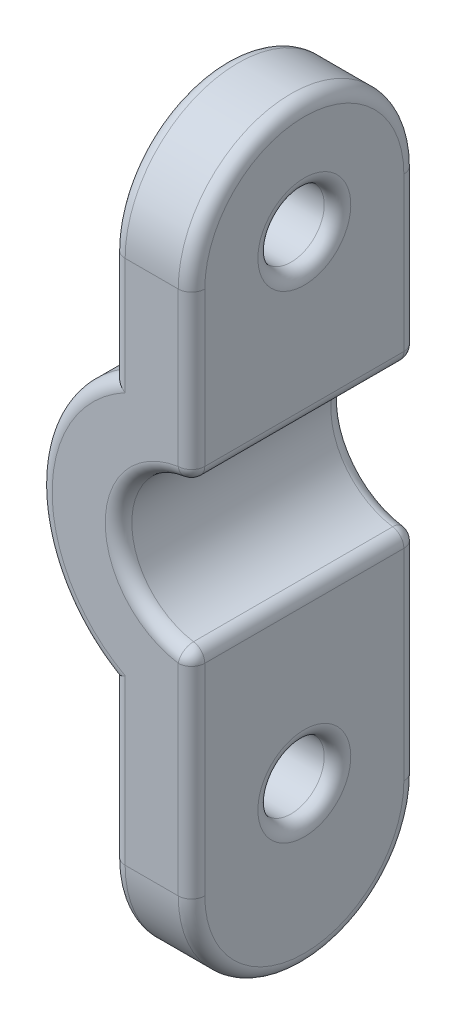
SolidWorks part; units mm, degrees
ref_plane "Front Plane" through (0, 0, 0) normal (0, 0, 1) x (1, 0, 0)
ref_plane "Top Plane" through (0, 0, 0) normal (0, 1, 0) x (1, 0, 0)
ref_plane "Right Plane" through (0, 0, 0) normal (1, 0, 0) x (0, 0, -1)
sketch "Sketch1" plane through (0, 0, 0) normal (0, 0, 1) x (1, 0, 0)
  line L0 (-2.75, 16.15) -> (-2.75, -14.35) construction
  line L1 (-2.75, -14.35) -> (-2.75, -1.85)
  line L6 (0.75, 11.15) -> (-2.75, 11.15) construction
  line L8 (1, 11.15) -> (0.5, 11.15) construction
  line L9 (-2.75, 16.15) -> (-5.75, 16.15)
  line L10 (-5.5, 0.9) -> (-8.5, 0.9) construction
  line L11 (-5.75, 16.15) -> (-5.75, 5.8054)
  line L12 (-2.75, -14.35) -> (-5.75, -14.35)
  line L13 (-5.75, -14.35) -> (-5.75, -4.0054)
  line L14 (-2.75, 16.15) -> (-2.75, 3.65)
  circle A0 centre (-2.75, 0.9) radius 2.75 construction
  circle A1 centre (-2.75, 0.9) radius 2.75 construction
  circle A2 centre (-2.75, 0.9) radius 5.75 construction
  arc A3 (-5.75, 5.8054) -> (-5.75, -4.0054) centre (-2.75, 0.9) ccw
  arc A4 (-2.75, 3.65) -> (-2.75, -1.85) centre (-2.75, 0.9) ccw
  point P5 (-2.75, 0.9)
  dimension "D1" = 5
  dimension "D2" = 3
  dimension "D3" = 3
extrude "Boss-Extrude1" add sketch "Sketch1" along normal blind 12.5 contours A4 L14 L9 L11 A3 L13 L12 L1
sketch "Sketch2" plane through (0, 0, 0) normal (1, 0, 0) x (0, 0, -1)
  line L0 (-6.25, 11.15) -> (-6.25, 14.15) construction
  line L1 (-2, 9.9) -> (-2, -9.9)
  line L2 (-10.5, 9.9) -> (-10.5, -9.9)
  line L3 (-2, 0) -> (-10.5, 0) construction
  line L5 (-12.5, 16.15) -> (0, 16.15)
  line L6 (-12.5, 16.15) -> (-12.5, -14.35)
  line L7 (-12.5, -14.35) -> (0, -14.35)
  line L8 (0, 16.15) -> (0, -14.35)
  arc A0 (-10.5, 9.9) -> (-2, 9.9) centre (-6.25, 9.9) cw
  circle A1 centre (-6.25, 9.9) radius 1.25 construction
  arc A2 (-10.5, -9.9) -> (-2, -9.9) centre (-6.25, -9.9) ccw
  circle A3 centre (-6.25, 9.9) radius 1.25
  circle A4 centre (-6.25, -8.1) radius 1.25
  dimension "D2" = 2.5
  dimension "D1" = 3
extrude "Cut-Extrude1" cut sketch "Sketch2" against normal through all contours L8 L5 L6 L7 A2 L2 A0 L1 | A3 | A4
fillet "Fillet1" radius 0.5 22 edges at (-2.75, -5.875, 10.5) (-2.75, -14.15, 6.25) (-2.75, 6.775, 10.5) (-2.75, 14.15, 6.25) (-5.75, -6.9527, 10.5) (-5.75, -14.15, 6.25) (-5.75, 7.8527, 2) (-5.75, 14.15, 6.25) (-5.5, 0.9, 10.5) (-2.75, -5.875, 2) (-5.5, 0.9, 2) (-2.75, 6.775, 2) (-5.75, 11.15, 6.25) (-5.75, -9.35, 6.25) (-5.75, -6.9527, 2) (-8.5, 0.9, 2) (-5.75, 7.8527, 10.5) (-8.5, 0.9, 10.5) (-2.75, -9.35, 6.25) (-2.75, 11.15, 6.25) (-2.75, -1.85, 6.25) (-2.75, 3.65, 6.25)
